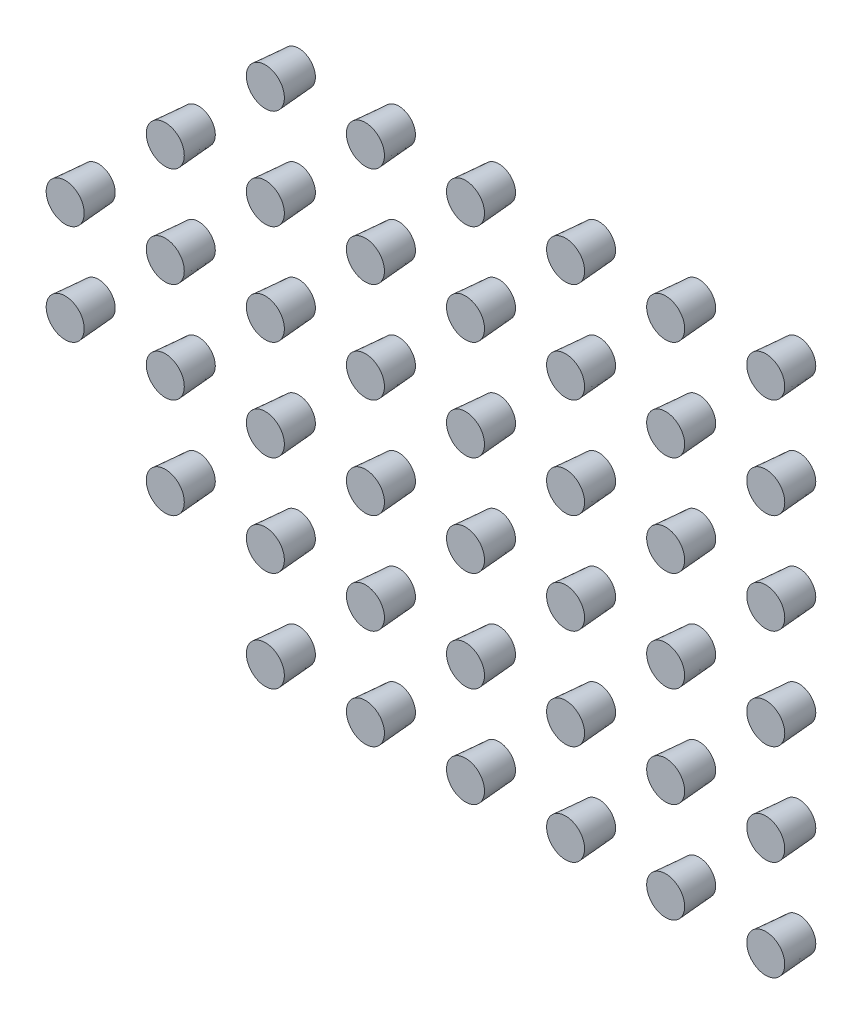
SolidWorks part; units mm, degrees
ref_plane "前视基准面" through (0, 0, 0) normal (0, 0, 1) x (1, 0, 0)
ref_plane "上视基准面" through (0, 0, 0) normal (0, 1, 0) x (1, 0, 0)
ref_plane "右视基准面" through (0, 0, 0) normal (1, 0, 0) x (0, 0, -1)
other "Configuration Table"
sketch "草图1" plane through (0, 0, 0) normal (0, 0, 1) x (1, 0, 0)
  circle A0 centre (0, 0) radius 0.5
  dimension "D1" = 1
extrude "凸台-拉伸1" add sketch "草图1" along normal blind 1 draft 4 draft outward yes
pattern_linear "阵列(线性)1" count 6 spacing 3 along (0, 1, 0) count 6 spacing 3 along (1, 0, 0) of "凸台-拉伸1"
ref_plane "基准面1" through (7.5, 0, 0) normal (1, 0, 0) x (0, 0, -1)
ref_plane "基准面2" through (0, 7.5, 0) normal (0, 1, 0) x (1, 0, 0)
pattern_linear "阵列(线性)2" count 2 spacing 3 along (-1, 0, 0) of bodies 110 109 108 107
pattern_linear "阵列(线性)3" count 2 spacing 3 along (-1, 0, 0) of bodies 143 144
